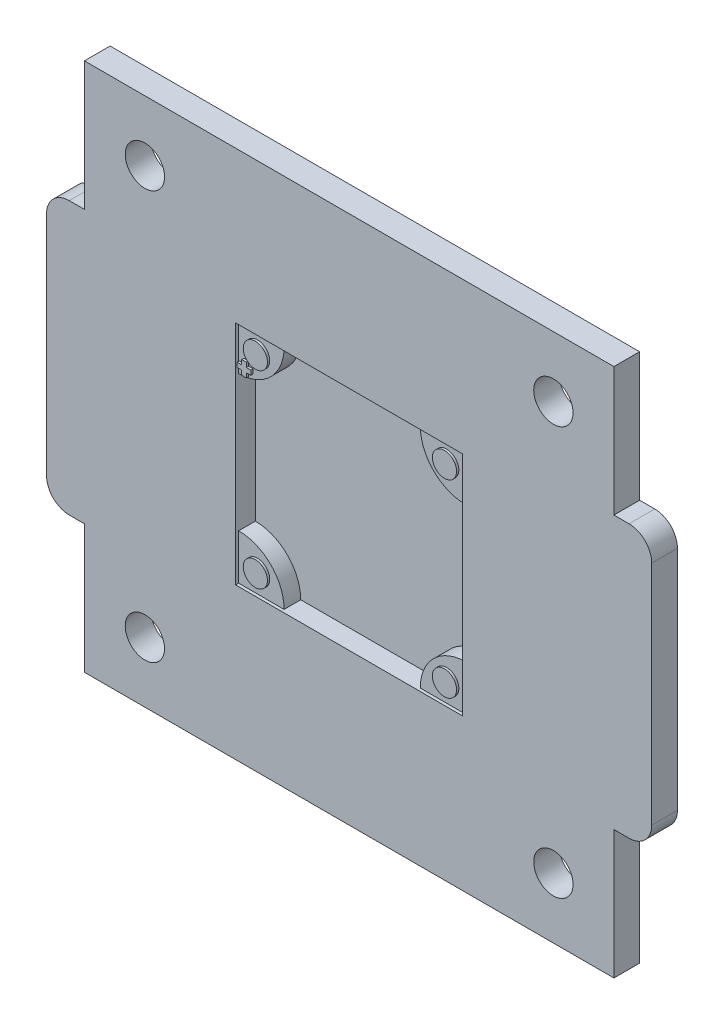
SolidWorks part; units mm, degrees
ref_plane "前视基准面" through (0, 0, 0) normal (0, 0, 1) x (1, 0, 0)
ref_plane "上视基准面" through (0, 0, 0) normal (0, 1, 0) x (1, 0, 0)
ref_plane "右视基准面" through (0, 0, 0) normal (1, 0, 0) x (0, 0, -1)
sketch "草图1" plane through (0, 0, 0) normal (0, 0, 1) x (1, 0, 0)
  line L0 (35, 70) -> (35, 0) construction
  line L1 (0, 0) -> (70, 0)
  line L2 (0, 0) -> (0, 70)
  line L3 (0, 70) -> (70, 70)
  line L4 (70, 0) -> (70, 70)
  line L5 (0, 35) -> (70, 35) construction
  line L6 (70, 17) -> (72, 17)
  line L7 (0, 53) -> (-2, 53)
  line L8 (0, 53) -> (0, 17)
  line L9 (0, 17) -> (-2, 17)
  line L10 (-5, 50) -> (-5, 20)
  line L11 (75, 50) -> (75, 20)
  line L12 (70, 53) -> (72, 53)
  line L13 (70, 53) -> (70, 17)
  arc A0 (-2, 17) -> (-5, 20) centre (-2, 20) cw
  arc A1 (-2, 53) -> (-5, 50) centre (-2, 50) ccw
  arc A2 (72, 17) -> (75, 20) centre (72, 20) ccw
  arc A3 (72, 53) -> (75, 50) centre (72, 50) cw
  point P6 (35, 70)
  point P10 (0, 35)
  point P15 (-5, 35)
  point P18 (-5, 17)
  point P21 (-5, 53)
  dimension "D4" = 3
  dimension "D1" = 70
  dimension "D2" = 5
  dimension "D3" = 36
extrude "凸台-拉伸1" add sketch "草图1" along normal blind 3.4 contours L7 A1 L10 A0 L9 L2 | L1 L4 L3 L2 | A3 L12 L4 L6 A2 L11
sketch "草图2" plane through (0, 0, 3.4) normal (0, 0, 1) x (1, 0, 0)
  line L0 (0, 70) -> (70, 70) construction
  line L1 (35, 70) -> (35, 0) construction
  line L2 (0, 0) -> (70, 0) construction
  line L3 (-5, 50) -> (-5, 20) construction
  line L4 (-5, 35) -> (75, 35) construction
  line L5 (75, 50) -> (75, 20) construction
  line L7 (20, 50) -> (50, 50)
  line L8 (20, 50) -> (20, 20)
  line L9 (20, 20) -> (50, 20)
  line L10 (50, 50) -> (50, 20)
  point P6 (35, 70)
  point P17 (35, 50)
  point P18 (20, 35)
  dimension "D1" = 30
extrude "切除-拉伸1" cut sketch "草图2" against normal blind 2.6
sketch "草图3" plane through (0, 0, 3.4) normal (0, 0, 1) x (1, 0, 0)
  line L0 (0, 70) -> (0, 0) construction
  line L1 (0, 70) -> (70, 70) construction
  line L2 (0, 53) -> (0, 70) construction
  line L3 (70, 0) -> (70, 70) construction
  line L4 (70, 53) -> (70, 70) construction
  line L5 (0, 35) -> (70, 35) construction
  line L6 (35, 70) -> (35, 0) construction
  line L7 (0, 0) -> (70, 0) construction
  circle A0 centre (8, 62) radius 2.6
  circle A1 centre (62, 62) radius 2.6
  circle A2 centre (8, 8) radius 2.6
  circle A3 centre (62, 8) radius 2.6
  point P18 (35, 70)
  point P19 (0, 35)
  dimension "D3" = 5.2
  dimension "D1" = 8
  dimension "D2" = 8
extrude "切除-拉伸2" cut sketch "草图3" against normal through all
sketch "草图4" plane through (0, 0, 0) normal (0, 0, 1) x (1, 0, 0)
  line L0 (20, 35) -> (50, 35) construction
  line L1 (20, 50) -> (50, 50) construction
  line L2 (20, 50) -> (20, 20) construction
  line L3 (20, 20) -> (50, 20) construction
  line L4 (50, 50) -> (50, 20) construction
  line L5 (35, 50) -> (35, 20) construction
  line L6 (20, 44) -> (20, 50)
  line L7 (20, 50) -> (26, 50)
  line L8 (50, 44) -> (50, 50)
  line L9 (50, 50) -> (44, 50)
  line L10 (50, 20) -> (44, 20)
  line L11 (50, 26) -> (50, 20)
  line L12 (20, 26) -> (20, 20)
  line L13 (20, 20) -> (26, 20)
  arc A0 (26, 50) -> (20, 44) centre (20, 50) cw
  arc A1 (44, 50) -> (50, 44) centre (50, 50) ccw
  arc A2 (44, 20) -> (50, 26) centre (50, 20) cw
  arc A3 (26, 20) -> (20, 26) centre (20, 20) ccw
  point P10 (35, 20)
  point P11 (20, 35)
  dimension "D1" = 6
extrude "凸台-拉伸2" add sketch "草图4" along normal blind 3
sketch "草图6" plane through (0, 0, 3) normal (0, 0, 1) x (1, 0, 0)
  line L0 (20, 35) -> (50, 35) construction
  line L1 (20, 50) -> (50, 50) construction
  line L2 (20, 50) -> (20, 20) construction
  line L3 (20, 20) -> (50, 20) construction
  line L4 (50, 50) -> (50, 20) construction
  line L5 (35, 50) -> (35, 20) construction
  line L6 (20.1, 45.5) -> (20.7, 45.5)
  line L7 (20.7, 45.5) -> (20.7, 46.1)
  line L8 (20.7, 46.1) -> (21.3, 46.1)
  line L9 (21.3, 46.1) -> (21.3, 45.5)
  line L10 (21.3, 45.5) -> (21.9, 45.5)
  line L11 (21.9, 45.5) -> (21.9, 44.9)
  line L12 (21.9, 44.9) -> (21.3, 44.9)
  line L13 (21.3, 44.9) -> (21.3, 44.3)
  line L14 (21.3, 44.3) -> (20.7, 44.3)
  line L15 (20.7, 44.3) -> (20.7, 44.9)
  line L16 (20.7, 44.9) -> (20.1, 44.9)
  line L17 (20.1, 44.9) -> (20.1, 45.5)
  circle A4 centre (22.5, 47.5) radius 1.6
  circle A5 centre (47.5, 47.5) radius 1.6
  circle A6 centre (47.5, 22.5) radius 1.6
  circle A7 centre (22.5, 22.5) radius 1.6
  point P10 (35, 20)
  point P11 (20, 35)
  point P31 (21, 46.1)
  dimension "D1" = 2.5
  dimension "D2" = 2.5
  dimension "D3" = 3.2
  dimension "D4" = 0.6
  dimension "D5" = 0.6
  dimension "D6" = 0.1
  dimension "D7" = 3.9
extrude "凸台-拉伸3" add sketch "草图6" along normal blind 0.3
